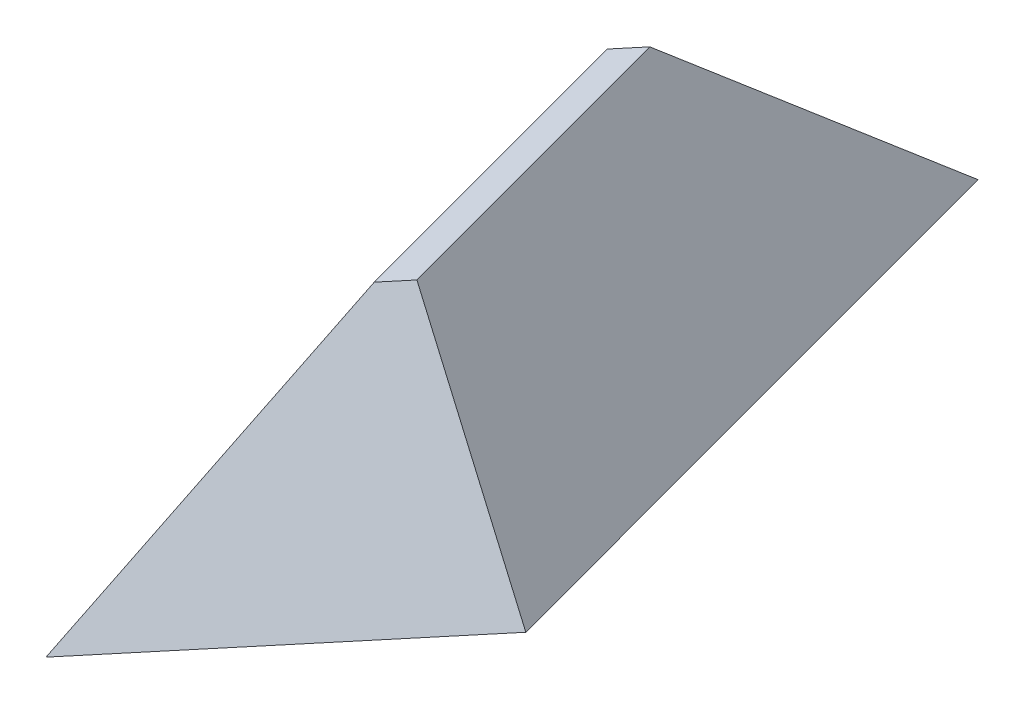
SolidWorks part; units mm, degrees
material "ABS"
ref_plane "Front Plane" through (0, 0, 0) normal (0, 0, 1) x (1, 0, 0)
ref_plane "Top Plane" through (0, 0, 0) normal (0, 1, 0) x (1, 0, 0)
ref_plane "Right Plane" through (0, 0, 0) normal (1, 0, 0) x (0, 0, -1)
sketch "Sketch1" plane through (0, 0, 0) normal (0, 1, 0) x (1, 0, 0)
  line L0 (-0.109, -9.098) -> (-2.3725, -0.6653)
  line L1 (-0.109, -9.098) -> (2.87, -5.5308)
  line L2 (-2.3725, -0.6653) -> (0.6065, 2.902)
  line L3 (2.87, -5.5308) -> (0.6065, 2.902)
  point P0 (2.87, -5.5308)
  dimension "D1" = 12
extrude "Boss-Extrude1" add sketch "Sketch1" along normal blind 3 draft 30
